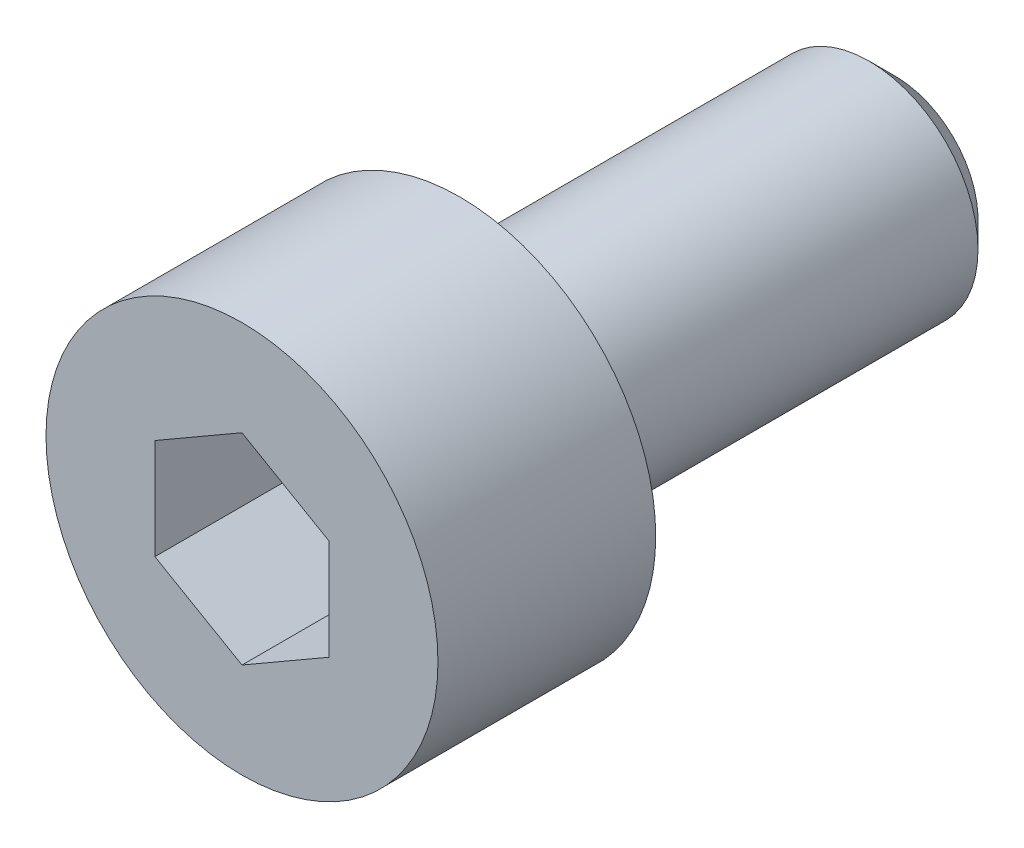
SolidWorks part; units mm, degrees
ref_plane "Front Plane" through (0, 0, 0) normal (0, 0, 1) x (1, 0, 0)
ref_plane "Top Plane" through (0, 0, 0) normal (0, 1, 0) x (1, 0, 0)
ref_plane "Right Plane" through (0, 0, 0) normal (1, 0, 0) x (0, 0, -1)
sketch "Sketch1" plane through (0, 0, 0) normal (0, 0, 1) x (1, 0, 0)
  circle A0 centre (0, 0) radius 2.25
  dimension "D1" = 4.5
extrude "Boss-Extrude1" add sketch "Sketch1" along normal blind 2.5
sketch "Sketch2" plane through (0, 0, 0) normal (0, 0, -1) x (-1, 0, 0)
  circle A0 centre (0, 0) radius 1.25
  dimension "D1" = 2.5
extrude "Boss-Extrude2" add sketch "Sketch2" along normal blind 5
chamfer "Chamfer1" distance 0.3 angle 45 1 edges at (-1.25, 0, -5)
sketch "Sketch3" plane through (0, 0, 2.5) normal (0, 0, 1) x (1, 0, 0)
  line L1 (0, 1.1547) -> (-1, 0.5774)
  line L2 (-1, 0.5774) -> (-1, -0.5774)
  line L3 (-1, -0.5774) -> (0, -1.1547)
  line L4 (0, -1.1547) -> (1, -0.5774)
  line L5 (1, -0.5774) -> (1, 0.5774)
  line L6 (1, 0.5774) -> (0, 1.1547)
  circle A0 centre (0, 0) radius 1 construction
  dimension "D1" = 2
extrude "Cut-Extrude1" cut sketch "Sketch3" against normal blind 2
